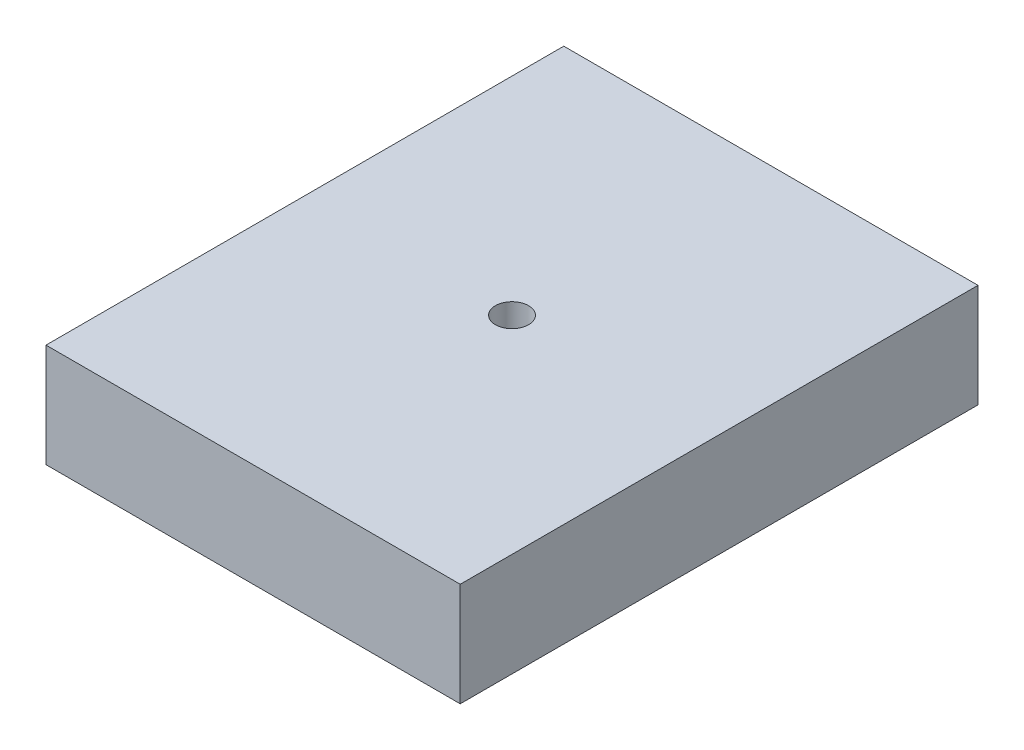
SolidWorks part; units mm, degrees
ref_plane "Plano frontal" through (0, 0, 0) normal (0, 0, 1) x (1, 0, 0)
ref_plane "Plano superior" through (0, 0, 0) normal (0, 1, 0) x (1, 0, 0)
ref_plane "Plano direito" through (0, 0, 0) normal (1, 0, 0) x (0, 0, -1)
sketch "Esboço1" plane through (0, 0, 0) normal (0, 1, 0) x (1, 0, 0)
  line L1 (-100, 0) -> (100, 0)
  line L2 (-100, 0) -> (-100, 250)
  line L3 (-100, 250) -> (100, 250)
  line L4 (100, 0) -> (100, 250)
  point P4 (0, 0)
  dimension "D1" = 200
  dimension "D2" = 250
extrude "Ressalto-extrusão1" add sketch "Esboço1" along normal blind 50
hole_wizard "Furo de diâmetro Ø16.0 (16)1" positions "Esboço3" profile "Esboço4" hole size "Ø16.0" standard "Ansi Metric" end condition through all
sketch "Esboço3" plane through (0, 50, 0) normal (0, 1, 0) x (1, 0, 0)
  line L0 (100, 250) -> (-100, 250) construction
  line L1 (100, 0) -> (100, 250) construction
  point P0 (0, 125)
  dimension "D1" = 125
  dimension "D2" = 100
sketch "Esboço4" plane through (0, 50, -125) normal (1, 0, 0) x (0, 0, 1)
  line L0 (0, 0) -> (0, 50)
  line L1 (0, 50) -> (8, 50)
  line L2 (8, 50) -> (8, 0)
  line L5 (8, 0) -> (0, 0)
  line L11 (0, -6.35) -> (0, 107.95) construction
  dimension "Thru Hole Dia." = 16
  dimension "Thru Hole Depth" = 50
sketch "Esboço5" plane through (0, 0, 0) normal (0, -1, 0) x (1, 0, 0)
  line L0 (0, -27) -> (0, -223)
  line L1 (3, -220) -> (3, -30)
  arc A0 (3, -30) -> (0, -27) centre (0, -30) ccw
  arc A2 (-3, -220) -> (3, -220) centre (0, -220) ccw construction
  arc A3 (0, -223) -> (3, -220) centre (0, -220) ccw
  dimension "D1" = 3
revolve "Corte-Revolução1" cut sketch "Esboço5" angle 360 about L0
sketch "Esboço6" plane through (0, 0, 0) normal (0, -1, 0) x (1, 0, 0)
  line L0 (-9, -34.85) -> (0, -34.85)
  line L1 (0, -34.85) -> (0, -31.85)
  line L2 (0, -31.85) -> (-6, -31.85)
  arc A0 (-6, -31.85) -> (-6, -37.85) centre (-6, -34.85) ccw construction
  arc A1 (-6, -31.85) -> (-9, -34.85) centre (-6, -34.85) ccw
revolve "Corte-Revolução2" cut sketch "Esboço6" angle 360 about L0
pattern_linear "Padrão linear1" count 3 spacing 30 along (0, 0, -1) count 2 spacing 120 along (0, 0, -1) of "Corte-Revolução2"
mirror "Espelhar1" about plane through (0, 0, 0) normal (1, 0, 0) of "Padrão linear1", "Corte-Revolução2"
sketch "Esboço7" plane through (0, 0, 0) normal (0, -1, 0) x (1, 0, 0)
  line L49 (-41.93, -30) -> (-40.9, -30)
  line L50 (-41.93, -30) -> (-41.93, -40.3)
  line L51 (-41.93, -40.3) -> (-40.9, -40.3)
  line L52 (-40.9, -30) -> (-40.9, -40.3)
  line L53 (-41.93, -60) -> (-40.9, -60)
  line L54 (-41.93, -60) -> (-41.93, -70.3)
  line L55 (-41.93, -70.3) -> (-40.9, -70.3)
  line L56 (-40.9, -60) -> (-40.9, -70.3)
  line L57 (-41.93, -90) -> (-40.9, -90)
  line L58 (-41.93, -90) -> (-41.93, -100.3)
  line L59 (-41.93, -100.3) -> (-40.9, -100.3)
  line L60 (-40.9, -90) -> (-40.9, -100.3)
  line L61 (-41.93, -149.7) -> (-40.9, -149.7)
  line L62 (-41.93, -149.7) -> (-41.93, -160)
  line L63 (-41.93, -160) -> (-40.9, -160)
  line L64 (-40.9, -149.7) -> (-40.9, -160)
  line L65 (-41.93, -179.7) -> (-40.9, -179.7)
  line L66 (-41.93, -179.7) -> (-41.93, -190)
  line L67 (-41.93, -190) -> (-40.9, -190)
  line L68 (-40.9, -179.7) -> (-40.9, -190)
  line L69 (-41.93, -209.7) -> (-40.9, -209.7)
  line L70 (-41.93, -209.7) -> (-41.93, -220)
  line L71 (-41.93, -220) -> (-40.9, -220)
  line L72 (-40.9, -209.7) -> (-40.9, -220)
  line L73 (40.9, -209.7) -> (41.93, -209.7)
  line L74 (40.9, -209.7) -> (40.9, -220)
  line L75 (40.9, -220) -> (41.93, -220)
  line L76 (41.93, -209.7) -> (41.93, -220)
  line L77 (40.9, -179.7) -> (41.93, -179.7)
  line L78 (40.9, -179.7) -> (40.9, -190)
  line L79 (40.9, -190) -> (41.93, -190)
  line L80 (41.93, -179.7) -> (41.93, -190)
  line L81 (40.9, -149.7) -> (41.93, -149.7)
  line L82 (40.9, -149.7) -> (40.9, -160)
  line L83 (40.9, -160) -> (41.93, -160)
  line L84 (41.93, -149.7) -> (41.93, -160)
  line L85 (40.9, -90) -> (41.93, -90)
  line L86 (40.9, -90) -> (40.9, -100.3)
  line L87 (40.9, -100.3) -> (41.93, -100.3)
  line L88 (41.93, -90) -> (41.93, -100.3)
  line L89 (40.9, -60) -> (41.93, -60)
  line L90 (40.9, -60) -> (40.9, -70.3)
  line L91 (40.9, -70.3) -> (41.93, -70.3)
  line L92 (41.93, -60) -> (41.93, -70.3)
  line L93 (40.9, -30) -> (41.93, -30)
  line L94 (40.9, -30) -> (40.9, -40.3)
  line L95 (40.9, -40.3) -> (41.93, -40.3)
  line L96 (41.93, -30) -> (41.93, -40.3)
extrude "Ressalto-extrusão2" add sketch "Esboço7" along normal blind 1
